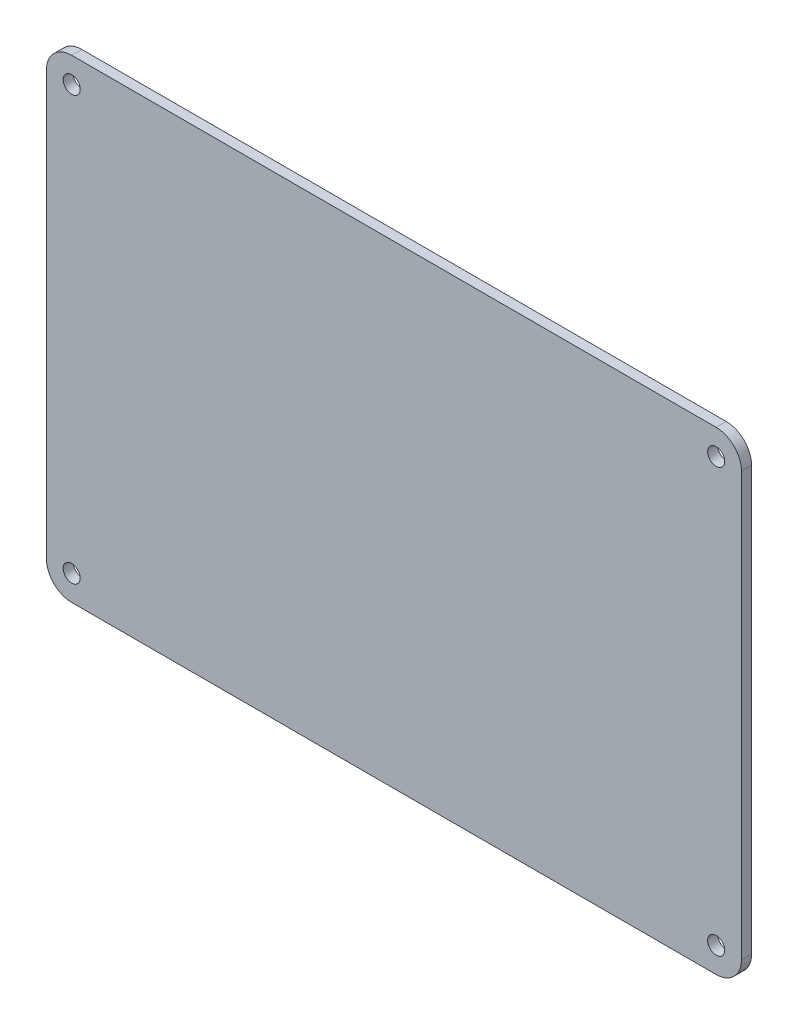
SolidWorks part; units mm, degrees
ref_plane "Front Plane" through (0, 0, 0) normal (0, 0, 1) x (1, 0, 0)
ref_plane "Top Plane" through (0, 0, 0) normal (0, 1, 0) x (1, 0, 0)
ref_plane "Right Plane" through (0, 0, 0) normal (1, 0, 0) x (0, 0, -1)
sketch "Sketch1" plane through (0, 0, 0) normal (0, 0, 1) x (1, 0, 0)
  line L1 (-51, -37.5) -> (51, -37.5)
  line L2 (-55, -33.5) -> (-55, 33.5)
  line L3 (-51, 37.5) -> (51, 37.5)
  line L4 (55, -33.5) -> (55, 33.5)
  line L5 (-55, -37.5) -> (55, 37.5) construction
  line L6 (-55, 37.5) -> (55, -37.5) construction
  arc A0 (-55, -33.5) -> (-51, -37.5) centre (-51, -33.5) ccw
  arc A1 (51, -37.5) -> (55, -33.5) centre (51, -33.5) ccw
  arc A2 (55, 33.5) -> (51, 37.5) centre (51, 33.5) ccw
  arc A3 (-55, 33.5) -> (-51, 37.5) centre (-51, 33.5) cw
  circle A4 centre (-51, 33.5) radius 1.35
  circle A5 centre (51, 33.5) radius 1.35
  circle A6 centre (51, -33.5) radius 1.35
  circle A7 centre (-51, -33.5) radius 1.35
  point P0 (0, 0)
  dimension "D3" = 4
  dimension "D4" = 2.7
  dimension "D1" = 75
  dimension "D2" = 110
extrude "Boss-Extrude1" add sketch "Sketch1" along normal blind 1.6
